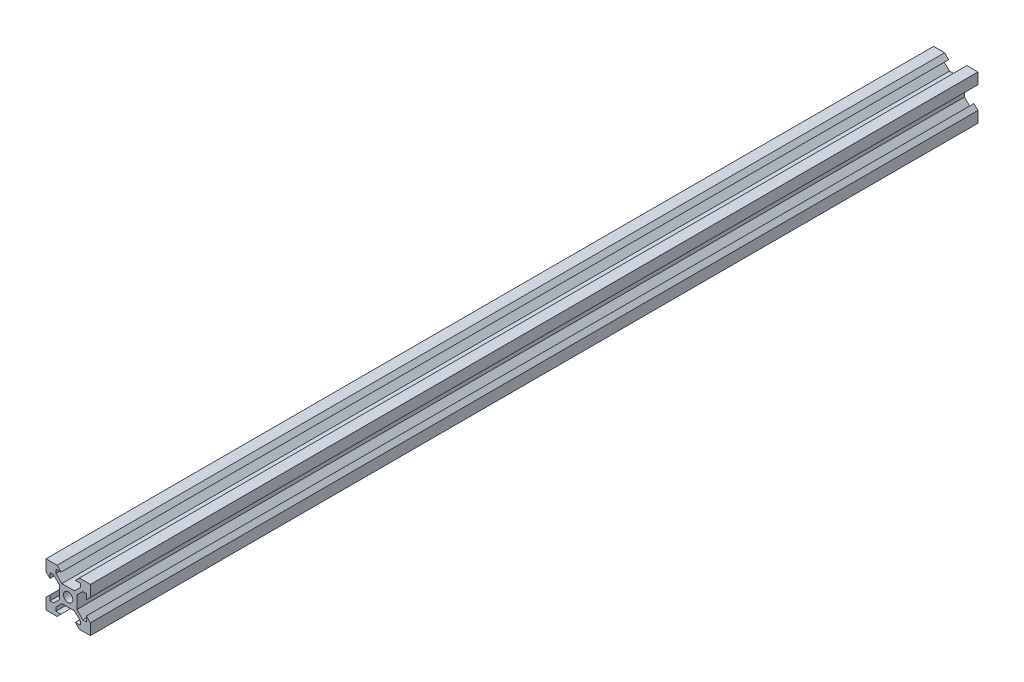
SolidWorks part; units mm, degrees
material "6063-T5"
ref_plane "Front Plane" through (0, 0, 0) normal (0, 0, 1) x (1, 0, 0)
ref_plane "Top Plane" through (0, 0, 0) normal (0, 1, 0) x (1, 0, 0)
ref_plane "Right Plane" through (0, 0, 0) normal (1, 0, 0) x (0, 0, -1)
sketch "Sketch1" plane through (0, 0, 0) normal (0, 0, 1) x (1, 0, 0)
  line L0 (-10, 10) -> (-5, 10)
  line L1 (10, -10) -> (-10, -10) construction
  line L2 (10, -10) -> (10, 10) construction
  line L3 (10, 10) -> (-10, 10) construction
  line L4 (-10, -10) -> (-10, 10) construction
  line L5 (10, -10) -> (-10, 10) construction
  line L6 (10, 10) -> (-10, -10) construction
  line L7 (-5, 10) -> (-3.2, 8.2)
  line L8 (-3.2, 8.2) -> (-5.4993, 8.2)
  line L9 (-5.4993, 8.2) -> (-5.4993, 6.56)
  line L10 (-2.84, 3.9007) -> (2.84, 3.9007)
  line L11 (0, 3.9007) -> (0, 2.1) construction
  line L12 (-5.4993, 6.56) -> (-2.84, 3.9007)
  line L13 (0, 0) -> (0, -13.2939) construction
  line L14 (0, 0) -> (-17.0802, 0) construction
  line L15 (-10, 10) -> (-10, 5)
  line L16 (-10, 5) -> (-8.2, 3.2)
  line L17 (-8.2, 3.2) -> (-8.2, 5.4993)
  line L18 (-8.2, 5.4993) -> (-6.56, 5.4993)
  line L19 (-6.56, 5.4993) -> (-3.9007, 2.84)
  line L20 (-3.9007, 2.84) -> (-3.9007, -2.84)
  line L21 (-3.2, -8.2) -> (-5.4993, -8.2)
  line L22 (-5.4993, -8.2) -> (-5.4993, -6.56)
  line L23 (-5, -10) -> (-3.2, -8.2)
  line L24 (-10, -10) -> (-5, -10)
  line L25 (-10, -10) -> (-10, -5)
  line L26 (-10, -5) -> (-8.2, -3.2)
  line L27 (-8.2, -3.2) -> (-8.2, -5.4993)
  line L28 (-8.2, -5.4993) -> (-6.56, -5.4993)
  line L29 (-6.56, -5.4993) -> (-3.9007, -2.84)
  line L30 (-5.4993, -6.56) -> (-2.84, -3.9007)
  line L31 (-2.84, -3.9007) -> (2.84, -3.9007)
  line L32 (5.4993, 6.56) -> (2.84, 3.9007)
  line L33 (3.2, 8.2) -> (5.4993, 8.2)
  line L34 (5.4993, 8.2) -> (5.4993, 6.56)
  line L35 (5, 10) -> (3.2, 8.2)
  line L36 (10, 10) -> (5, 10)
  line L37 (10, 10) -> (10, 5)
  line L38 (10, 5) -> (8.2, 3.2)
  line L39 (8.2, 3.2) -> (8.2, 5.4993)
  line L40 (8.2, 5.4993) -> (6.56, 5.4993)
  line L41 (6.56, 5.4993) -> (3.9007, 2.84)
  line L42 (3.9007, 2.84) -> (3.9007, -2.84)
  line L43 (6.56, -5.4993) -> (3.9007, -2.84)
  line L44 (8.2, -5.4993) -> (6.56, -5.4993)
  line L45 (8.2, -3.2) -> (8.2, -5.4993)
  line L46 (10, -5) -> (8.2, -3.2)
  line L47 (10, -10) -> (10, -5)
  line L48 (10, -10) -> (5, -10)
  line L49 (5, -10) -> (3.2, -8.2)
  line L50 (3.2, -8.2) -> (5.4993, -8.2)
  line L51 (5.4993, -8.2) -> (5.4993, -6.56)
  line L52 (5.4993, -6.56) -> (2.84, -3.9007)
  circle A0 centre (0, 0) radius 2.1
  arc A1 (0, -2.1) -> (0, 2.1) centre (0, 0) cw construction
  point P0 (0, 0)
  point P25 (-3.9007, 0)
  point P35 (0, 0)
  point P56 (0, -3.9007)
  dimension "D2" = 4.2
  dimension "D1" = 20
  dimension "D3" = 1.64
  dimension "D4" = 1.8
  dimension "D5" = 45
  dimension "D6" = 1.5
  dimension "D7" = 5.68
  dimension "D8" = 5
extrude "Boss-Extrude1" add sketch "Sketch1" along normal mid plane 400
